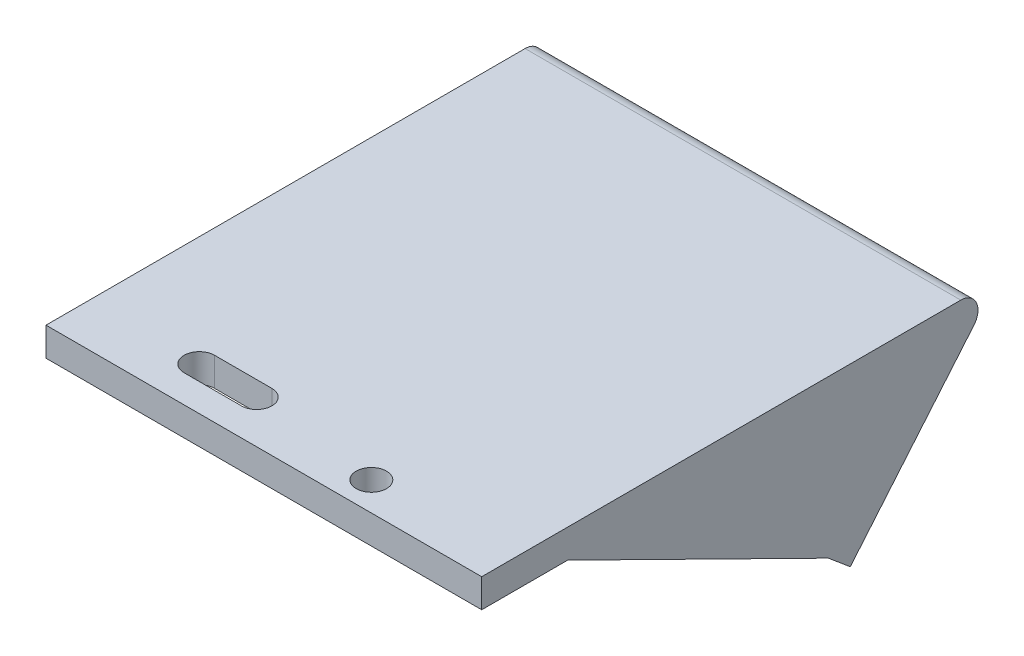
SolidWorks part; units mm, degrees
ref_plane "前视基准面" through (0, 0, 0) normal (0, 0, 1) x (1, 0, 0)
ref_plane "上视基准面" through (0, 0, 0) normal (0, 1, 0) x (1, 0, 0)
ref_plane "右视基准面" through (0, 0, 0) normal (1, 0, 0) x (0, 0, -1)
sketch "草图1" plane through (0, 0, 0) normal (1, 0, 0) x (0, 0, -1)
  line L0 (0, 0) -> (90, 0)
  line L1 (90, 0) -> (64.2885, -30.6418)
  line L2 (64.2885, -30.6418) -> (60.4583, -27.4278)
  line L3 (0, 0) -> (0, -5)
  line L4 (0, -5) -> (79.2775, -5)
  line L5 (60.4583, -27.4278) -> (79.2775, -5)
  dimension "D1" = 5
  dimension "D2" = 90
  dimension "D3" = 40
  dimension "D4" = 50
extrude "凸台-拉伸1" add sketch "草图1" along normal blind 70
sketch "草图2" plane through (0, -41.1024, -48.9839) normal (0, 0.6428, 0.766) x (1, 0, 0)
  line L0 (35, 17.8509) -> (35, 27.8509) construction
  line L1 (70, 17.8509) -> (0, 17.8509) construction
  line L2 (12.5, 27.8509) -> (57.5, 27.8509) construction
  circle A0 centre (12.5, 27.8509) radius 1.65
  circle A1 centre (57.5, 27.8509) radius 1.65
  point P6 (35, 27.8509)
  dimension "D3" = 3.3
  dimension "D1" = 10
  dimension "D2" = 45
extrude "切除-拉伸1" cut sketch "草图2" against normal through all
sketch "草图3" plane through (0, 0, 0) normal (0, 1, 0) x (1, 0, 0)
  line L0 (35, 15) -> (35, 0) construction
  line L1 (17.5, 10) -> (52.5, 10) construction
  line L2 (17.5, 10) -> (17.5, 20) construction
  line L3 (17.5, 20) -> (52.5, 20) construction
  line L4 (52.5, 10) -> (52.5, 20) construction
  line L5 (17.5, 10) -> (52.5, 20) construction
  line L6 (17.5, 20) -> (52.5, 10) construction
  line L7 (70, 0) -> (0, 0) construction
  circle A0 centre (17.5, 20) radius 1.65
  circle A1 centre (17.5, 10) radius 1.65
  circle A2 centre (52.5, 10) radius 1.65
  circle A3 centre (52.5, 20) radius 1.65
  point P0 (35, 15)
  dimension "D4" = 3.3
  dimension "D1" = 10
  dimension "D2" = 35
  dimension "D3" = 15
extrude "切除-拉伸2" [suppressed] cut sketch "草图3" against normal up to next
fillet "圆角1" radius 3 2 edges at (35, 0, -90) (35, -5, -79.2775)
sketch "草图5" plane through (0, 0, 0) normal (0, 1, 0) x (1, 0, 0)
  line L0 (35, 0) -> (35, 5) construction
  line L1 (70, 0) -> (0, 0) construction
  line L2 (10, 5) -> (60, 5) construction
  line L3 (10, 7.25) -> (60, 7.25)
  line L4 (10, 2.75) -> (60, 2.75)
  arc A0 (10, 7.25) -> (10, 2.75) centre (10, 5) ccw
  arc A1 (60, 2.75) -> (60, 7.25) centre (60, 5) ccw
  point P6 (35, 5)
  dimension "D1" = 50
  dimension "D2" = 4.5
  dimension "D3" = 5
extrude "切除-拉伸3" [suppressed] cut sketch "草图5" against normal through all
sketch "草图6" plane through (0, 0, 0) normal (0, 1, 0) x (1, 0, 0)
  line L0 (35, 0) -> (35, 5) construction
  line L1 (70, 0) -> (0, 0) construction
  line L2 (21.25, 5) -> (48.75, 5) construction
  circle A0 centre (48.75, 5) radius 2.65
  point P7 (35, 5)
  dimension "D3" = 5.3
  dimension "D1" = 5
  dimension "D2" = 27.5
extrude "切除-拉伸4" cut sketch "草图6" against normal through all
ref_plane "基准面1" through (35, 0, 0) normal (-1, 0, 0) x (0, 0, 1)
sketch "草图7" plane through (0, 0, 0) normal (-1, 0, 0) x (0, 0, 1)
  line L0 (-60.4583, -27.4278) -> (-15, -5)
  line L6 (0, 0) -> (-83.5665, 0)
  line L7 (-85.8646, -4.9284) -> (-64.2885, -30.6418)
  line L8 (-64.2885, -30.6418) -> (-60.4583, -27.4278)
  line L9 (-60.4583, -27.4278) -> (-75.1421, -9.9284)
  line L10 (-72.8439, -5) -> (0, -5)
  line L11 (0, -5) -> (0, 0)
  line L12 (0, 0) -> (-83.5665, 0)
  line L13 (-85.8646, -4.9284) -> (-64.2885, -30.6418)
  line L14 (-64.2885, -30.6418) -> (-60.4583, -27.4278)
  line L15 (-60.4583, -27.4278) -> (-75.1421, -9.9284)
  line L16 (-72.8439, -5) -> (0, -5)
  line L17 (0, -5) -> (0, 0)
  arc A2 (-83.5665, 0) -> (-85.8646, -4.9284) centre (-83.5665, -3) ccw
  arc A3 (-72.8439, -5) -> (-75.1421, -9.9284) centre (-72.8439, -8) ccw
  arc A4 (-83.5665, 0) -> (-85.8646, -4.9284) centre (-83.5665, -3) ccw
  arc A5 (-72.8439, -5) -> (-75.1421, -9.9284) centre (-72.8439, -8) ccw
  dimension "D2" = 15
  dimension "D1" = 0
extrude "凸台-拉伸2" add sketch "草图7" along normal blind 3
mirror "镜向1" about plane through (35, 0, 0) normal (-1, 0, 0) of "凸台-拉伸2"
sketch "草图8" plane through (0, 0, 0) normal (0, 1, 0) x (1, 0, 0)
  line L0 (35, 0) -> (35, 5) construction
  line L1 (73, 0) -> (-3, 0) construction
  line L2 (35, 5) -> (48.75, 5) construction
  line L3 (21.25, 5) -> (48.75, 5) construction
  line L4 (21.25, 5) -> (21.25, 7.5) construction
  line L5 (16.25, 7.5) -> (26.25, 7.5) construction
  line L6 (16.25, 10.15) -> (26.25, 10.15)
  line L7 (16.25, 4.85) -> (26.25, 4.85)
  arc A0 (16.25, 10.15) -> (16.25, 4.85) centre (16.25, 7.5) ccw
  arc A1 (26.25, 4.85) -> (26.25, 10.15) centre (26.25, 7.5) ccw
  point P9 (35, 5)
  point P11 (21.25, 7.5)
  point P12 (21.25, 7.5)
  point P17 (0, 0)
  dimension "D1" = 2.5
  dimension "D2" = 5.3
  dimension "D3" = 10
extrude "切除-拉伸5" cut sketch "草图8" against normal through all
